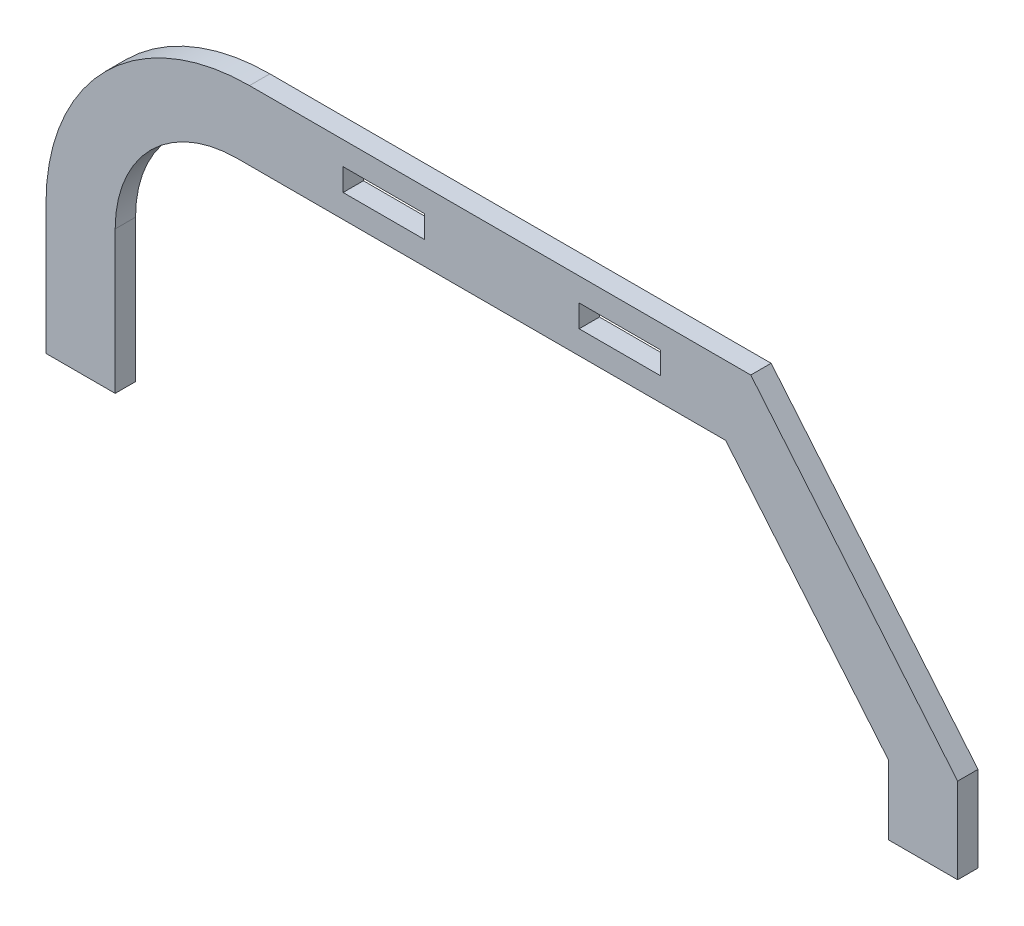
SolidWorks part; units mm, degrees
ref_plane "Plan de face" through (0, 0, 0) normal (0, 0, 1) x (1, 0, 0)
ref_plane "Plan de dessus" through (0, 0, 0) normal (0, 1, 0) x (1, 0, 0)
ref_plane "Plan de droite" through (0, 0, 0) normal (1, 0, 0) x (0, 0, -1)
sketch "Sketch1" plane through (0, 0, 0) normal (0, 0, 1) x (1, 0, 0)
  line L0 (0, 0) -> (0, 82) construction
  line L1 (-112, 0) -> (-95, 0)
  line L2 (-95, 0) -> (-95, 17)
  line L3 (-95, 17) -> (-95, 35)
  line L4 (-55, 65) -> (55, 65)
  line L5 (-112, 0) -> (-112, 21)
  line L6 (-112, 21) -> (-112, 32)
  line L7 (-61.1667, 82) -> (61.1667, 82)
  line L8 (19, 76.25) -> (19, 70.75)
  line L9 (-39, 76.25) -> (-19, 76.25)
  line L10 (-39, 76.25) -> (-39, 70.75)
  line L11 (-39, 70.75) -> (-19, 70.75)
  line L12 (-19, 76.25) -> (-19, 70.75)
  line L13 (39, 70.75) -> (19, 70.75)
  line L14 (39, 76.25) -> (39, 70.75)
  line L15 (39, 76.25) -> (19, 76.25)
  line L16 (112, 21) -> (61.1667, 82)
  line L17 (112, 0) -> (112, 21)
  line L18 (95, 17) -> (55, 65)
  line L19 (95, 0) -> (95, 17)
  line L20 (112, 0) -> (95, 0)
  line L21 (0, 82) -> (0, 65) construction
  line L22 (-62, 82) -> (-61.1667, 82)
  line L23 (0, 82) -> (0, 65) construction
  line L24 (-65, 65) -> (-55, 65)
  line L25 (0, 65) -> (0, 82) construction
  arc A0 (-112, 32) -> (-62, 82) centre (-62, 32) cw
  arc A1 (-65, 65) -> (-95, 35) centre (-65, 35) ccw
  point P22 (0, 65)
  dimension "D15" = 50
  dimension "D16" = 30
  dimension "D1" = 17
  dimension "D2" = 5.5
  dimension "D3" = 224
  dimension "D4" = 65
  dimension "D5" = 17
  dimension "D6" = 17
  dimension "D7" = 21
  dimension "D8" = 16
  dimension "D9" = 5.75
  dimension "D10" = 20
  dimension "D11" = 40
  dimension "D12" = 19
  dimension "D13" = 122.3333
  dimension "D14" = 110
extrude "Boss-Extrude1" add sketch "Sketch1" along normal blind 5
